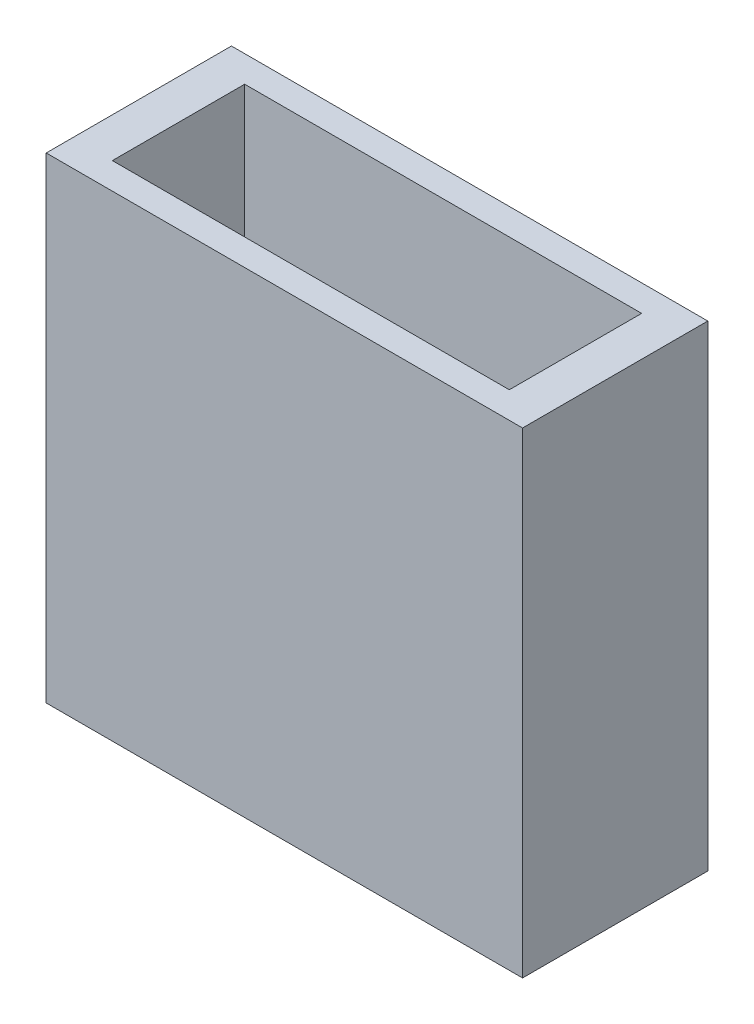
SolidWorks part; units mm, degrees
ref_plane "Front Plane" through (0, 0, 0) normal (0, 0, 1) x (1, 0, 0)
ref_plane "Top Plane" through (0, 0, 0) normal (0, 1, 0) x (1, 0, 0)
ref_plane "Right Plane" through (0, 0, 0) normal (1, 0, 0) x (0, 0, -1)
sketch "Sketch1" plane through (0, 0, 0) normal (0, 1, 0) x (1, 0, 0)
  line L1 (0, 0) -> (45.72, 0)
  line L2 (0, 0) -> (0, 17.78)
  line L3 (0, 17.78) -> (45.72, 17.78)
  line L4 (45.72, 0) -> (45.72, 17.78)
  dimension "D1" = 45.72
  dimension "D2" = 17.78
extrude "Boss-Extrude1" add sketch "Sketch1" along normal blind 45.72
ref_plane "Plane1" through (0, 45.72, 0) normal (0, 1, 0) x (1, 0, 0)
sketch "Sketch2" plane through (0, 45.72, 0) normal (0, 1, 0) x (1, 0, 0)
  line L0 (0, 17.78) -> (0, 0) construction
  line L1 (3.81, 2.54) -> (41.91, 2.54)
  line L2 (3.81, 2.54) -> (3.81, 15.24)
  line L3 (3.81, 15.24) -> (41.91, 15.24)
  line L4 (41.91, 2.54) -> (41.91, 15.24)
  line L5 (45.72, 0) -> (45.72, 17.78) construction
  line L6 (0, 0) -> (45.72, 0) construction
  line L7 (45.72, 17.78) -> (0, 17.78) construction
  dimension "D1" = 3.81
  dimension "D2" = 3.81
  dimension "D3" = 2.54
  dimension "D4" = 2.54
extrude "Cut-Extrude1" cut sketch "Sketch2" against normal blind 41.91
sketch "Sketch3" plane through (0, 0, 0) normal (0, 1, 0) x (1, 0, 0)
  line L0 (45.72, 0) -> (45.72, 17.78) construction
  line L1 (45.72, 17.78) -> (0, 17.78) construction
  circle A0 centre (22.86, 8.89) radius 2.4765
  circle A1 centre (17.018, 8.89) radius 2.54
  circle A2 centre (28.702, 8.89) radius 2.54
  dimension "D1" = 4.953
  dimension "D4" = 5.08
  dimension "D5" = 5.08
  dimension "D2" = 22.86
  dimension "D3" = 8.89
  dimension "D6" = 5.842
  dimension "D7" = 5.842
  dimension "D8" = 8.89
  dimension "D9" = 8.89
extrude "Cut-Extrude2" cut sketch "Sketch3" along normal through all
equation "\"x\"=0.296138"
